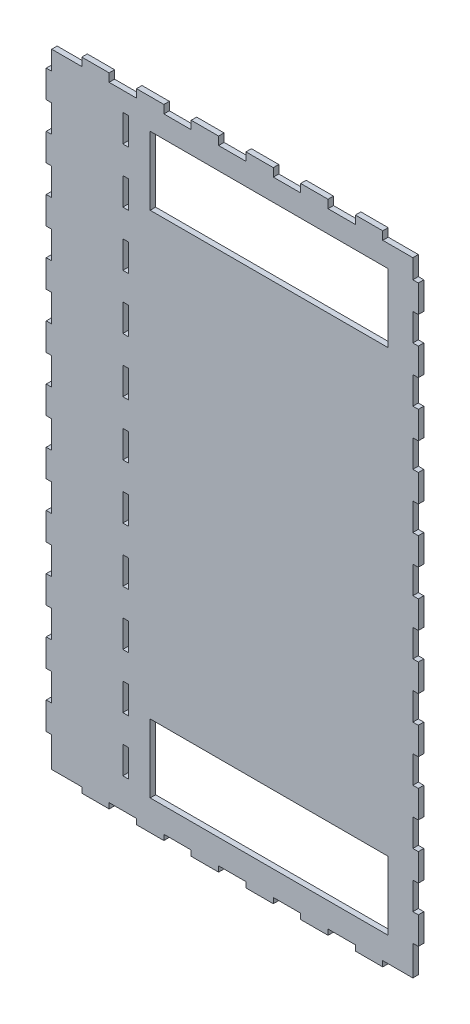
SolidWorks part; units mm, degrees
ref_plane "Front Plane" through (0, 0, 0) normal (0, 0, 1) x (1, 0, 0)
ref_plane "Top Plane" through (0, 0, 0) normal (0, 1, 0) x (1, 0, 0)
ref_plane "Right Plane" through (0, 0, 0) normal (1, 0, 0) x (0, 0, -1)
sketch "Sketch1" plane through (0, 0, 0) normal (0, 0, 1) x (1, 0, 0)
  line L0 (0, 113.5) -> (130, 113.5) construction
  line L1 (0, 0) -> (130, 0)
  line L2 (0, 0) -> (0, 227)
  line L3 (0, 227) -> (130, 227)
  line L4 (130, 0) -> (130, 227)
  line L5 (35, 8) -> (122, 8)
  line L6 (35, 8) -> (35, 33)
  line L7 (35, 33) -> (122, 33)
  line L8 (122, 8) -> (122, 33)
  line L9 (35, 194) -> (122, 194)
  line L10 (122, 219) -> (122, 194)
  line L11 (35, 219) -> (122, 219)
  line L12 (35, 219) -> (35, 194)
  dimension "D1" = 130
  dimension "D2" = 227
  dimension "D3" = 35
  dimension "D4" = 8
  dimension "D5" = 8
  dimension "D6" = 25
extrude "Boss-Extrude1" add sketch "Sketch1" along normal blind 2
sketch "Sketch2" plane through (0, 0, 0) normal (0, -1, 0) x (1, 0, 0)
  line L0 (0, 0) -> (130, 0) construction
  line L1 (10, 0) -> (20, 0)
  line L2 (10, 0) -> (10, 2)
  line L3 (10, 2) -> (20, 2)
  line L4 (20, 0) -> (20, 2)
  line L5 (0, 2) -> (130, 2) construction
  line L6 (0, 2) -> (0, 0) construction
  dimension "D1" = 10
  dimension "D2" = 10
extrude "Boss-Extrude2" add sketch "Sketch2" along normal blind 3
pattern_linear "LPattern1" count 6 spacing 20 along (1, 0, 0) of "Boss-Extrude2"
sketch "Sketch3" plane through (0, 227, 0) normal (0, 1, 0) x (1, 0, 0)
  line L0 (130, -2) -> (0, -2) construction
  line L1 (10, -2) -> (20, -2)
  line L2 (10, -2) -> (10, 0)
  line L3 (10, 0) -> (20, 0)
  line L4 (20, -2) -> (20, 0)
  line L5 (130, 0) -> (0, 0) construction
  line L6 (0, -2) -> (0, 0) construction
  dimension "D1" = 10
  dimension "D2" = 10
extrude "Boss-Extrude3" add sketch "Sketch3" along normal blind 3
pattern_linear "LPattern2" count 6 spacing 20 along (1, 0, 0) of "Boss-Extrude3"
sketch "Sketch4" plane through (130, 0, 0) normal (1, 0, 0) x (0, 0, -1)
  line L0 (-2, 0) -> (-2, 227) construction
  line L1 (-2, 10) -> (0, 10)
  line L2 (-2, 10) -> (-2, 20)
  line L3 (-2, 20) -> (0, 20)
  line L4 (0, 10) -> (0, 20)
  line L5 (0, 0) -> (0, 227) construction
  line L6 (0, 0) -> (-2, 0) construction
  dimension "D1" = 10
  dimension "D2" = 10
extrude "Boss-Extrude4" add sketch "Sketch4" along normal blind 3
pattern_linear "LPattern3" count 11 spacing 20 along (0, 1, 0) of "Boss-Extrude4"
sketch "Sketch5" plane through (0, 0, 0) normal (-1, 0, 0) x (0, 0, 1)
  line L0 (0, 227) -> (0, 0) construction
  line L1 (2, 227) -> (2, 0) construction
  line L2 (0, 10) -> (2, 10)
  line L3 (0, 10) -> (0, 20)
  line L4 (0, 20) -> (2, 20)
  line L5 (2, 10) -> (2, 20)
  line L6 (2, 0) -> (0, 0) construction
  dimension "D1" = 10
  dimension "D2" = 10
extrude "Boss-Extrude5" add sketch "Sketch5" along normal blind 3
pattern_linear "LPattern4" count 11 spacing 20 along (0, 1, 0) of "Boss-Extrude5"
sketch "Sketch6" plane through (0, 0, 2) normal (0, 0, 1) x (1, 0, 0)
  line L0 (0, 70) -> (0, 60) construction
  line L1 (25, 10) -> (28, 10)
  line L2 (25, 10) -> (25, 20)
  line L3 (25, 20) -> (28, 20)
  line L4 (28, 10) -> (28, 20)
  line L5 (20, 0) -> (30, 0) construction
  dimension "D1" = 25
  dimension "D2" = 3
  dimension "D3" = 10
  dimension "D4" = 10
extrude "Cut-Extrude1" cut sketch "Sketch6" against normal blind 3
pattern_linear "LPattern5" count 11 spacing 20 along (0, 1, 0) of "Cut-Extrude1"
sketch "Esquisse1" plane through (0, 0, 2) normal (0, 0, 1) x (1, 0, 0)
  line L0 (25, 10) -> (28, 10) construction
  line L1 (0, 227) -> (-1, 227)
  line L2 (0, 227) -> (0, 0)
  line L3 (0, 0) -> (-1, 0)
  line L4 (-1, 227) -> (-1, 0)
  line L5 (-1, 0) -> (130, 0)
  line L6 (-1, 0) -> (-1, -1)
  line L7 (-1, -1) -> (130, -1)
  line L8 (130, 0) -> (130, -1)
  line L9 (130, -1) -> (131, -1)
  line L10 (130, -1) -> (130, 227)
  line L11 (130, 227) -> (131, 227)
  line L12 (131, -1) -> (131, 227)
  line L13 (28, 220) -> (27, 220)
  line L14 (28, 220) -> (28, 10)
  line L15 (28, 10) -> (27, 10)
  line L16 (27, 220) -> (27, 10)
  dimension "D1" = 1
  dimension "D2" = 1
  dimension "D3" = 1
  dimension "D4" = 1
extrude "Boss.-Extru.1" add sketch "Esquisse1" against normal blind 2 contours L8 L5 L3 L6 L7 | L13 L16 L15 L14 | L1 L4 L3 L2 | L9 L12 L11 L10 L8
